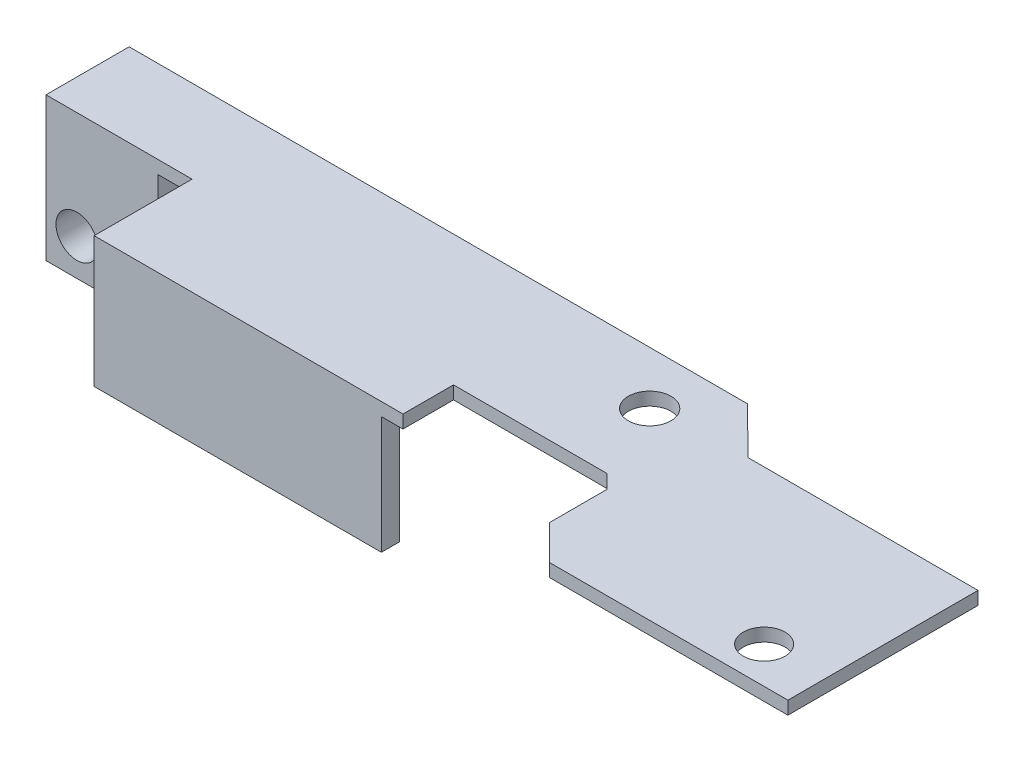
SolidWorks part; units mm, degrees
ref_plane "前视基准面" through (0, 0, 0) normal (0, 0, 1) x (1, 0, 0)
ref_plane "上视基准面" through (0, 0, 0) normal (0, 1, 0) x (1, 0, 0)
ref_plane "右视基准面" through (0, 0, 0) normal (1, 0, 0) x (0, 0, -1)
sketch "草图1" plane through (0, 0, 0) normal (0, 1, 0) x (1, 0, 0)
  line L0 (-59.2591, 5) -> (-10.5929, 5)
  line L2 (10.5929, -5) -> (10.5929, 1.4523)
  line L5 (-11.3641, -4.9974) -> (-11.3641, -5)
  line L6 (-10.5929, 5) -> (-7.0332, 1.4523)
  line L7 (-59.2591, 5) -> (-59.2591, 0)
  line L8 (-59.2591, 0) -> (-59.2591, -2.3664)
  line L9 (-59.2591, -2.3664) -> (-46.772, -2.3664)
  line L10 (-46.772, -2.3664) -> (-46.772, -8.8664)
  line L11 (-46.772, -8.8664) -> (-23.12, -8.8664)
  line L12 (-23.12, -8.8664) -> (-23.12, -5)
  line L13 (-23.12, -5) -> (-11.3641, -5)
  line L14 (10.5929, -5) -> (10.5929, -13.1053)
  line L15 (10.5929, -13.1053) -> (-7.649, -13.1053)
  line L16 (-7.649, -13.1053) -> (-10.3117, -10.4425)
  line L17 (-10.3117, -10.4425) -> (-10.3117, -6.0497)
  line L18 (-10.3117, -6.0497) -> (-11.3641, -4.9974)
  line L20 (-7.0332, 1.4523) -> (10.5929, 1.4523)
  circle A0 centre (-14.0394, 0.9427) radius 1.6326
  circle A1 centre (5.9688, -10.3003) radius 1.6
  point P0 (0, 0)
  point P14 (5.9688, -10.3003)
  point P16 (-13.8769, 0.9858)
  point P18 (-14.0394, 0.9427)
  dimension "D1" = 6.5
extrude "凸台-拉伸1" add sketch "草图1" along normal blind 1
sketch "草图2" plane through (0, 0, 0) normal (0, -1, 0) x (1, 0, 0)
  line L1 (-46.772, 8.8664) -> (-24.7756, 8.8664)
  line L2 (-46.772, 8.8664) -> (-46.772, 7.4664)
  line L3 (-46.772, 7.4664) -> (-24.7756, 7.4664)
  line L4 (-24.7756, 8.8664) -> (-24.7756, 7.4664)
  dimension "D1" = 1.4
extrude "凸台-拉伸2" add sketch "草图2" along normal blind 9
sketch "草图3" plane through (0, 0, 0) normal (0, -1, 0) x (1, 0, 0)
  line L0 (-10.5929, -5) -> (-59.2591, -5) construction
  line L1 (-59.2591, 2.3664) -> (-49.3972, 2.3664)
  line L2 (-59.2591, 2.3664) -> (-59.2591, -5)
  line L3 (-59.2591, -5) -> (-49.3972, -5)
  line L4 (-49.3972, 2.3664) -> (-49.3972, -5)
extrude "凸台-拉伸3" add sketch "草图3" along normal blind 10
sketch "草图5" plane through (0, 0, 2.3664) normal (0, 0, 1) x (1, 0, 0)
  circle A0 centre (-55.5949, -7.2) radius 1.6
  dimension "D1" = 3.2
extrude "切除-拉伸1" cut sketch "草图5" against normal up to next
sketch "草图6" plane through (0, 1, 0) normal (0, 1, 0) x (1, 0, 0)
  line L0 (-59.2591, -2.3664) -> (-46.772, -2.3664) construction
  line L1 (-59.2591, 5) -> (-57.9591, 5)
  line L2 (-59.2591, 5) -> (-59.2591, -2.3664)
  line L3 (-59.2591, -2.3664) -> (-57.9591, -2.3664)
  line L4 (-57.9591, 5) -> (-57.9591, -1.3664)
  line L6 (-57.9591, -2.3664) -> (-46.772, -2.3664)
  line L8 (-57.9591, -1.3664) -> (-46.772, -1.3664)
  line L9 (-46.772, -2.3664) -> (-46.772, -1.3664)
  line L10 (-46.772, -2.3664) -> (-46.772, -8.8664) construction
  dimension "D1" = 1.3
  dimension "D2" = 0
  dimension "D3" = 1
extrude "切除-拉伸2" cut sketch "草图6" against normal up to next
